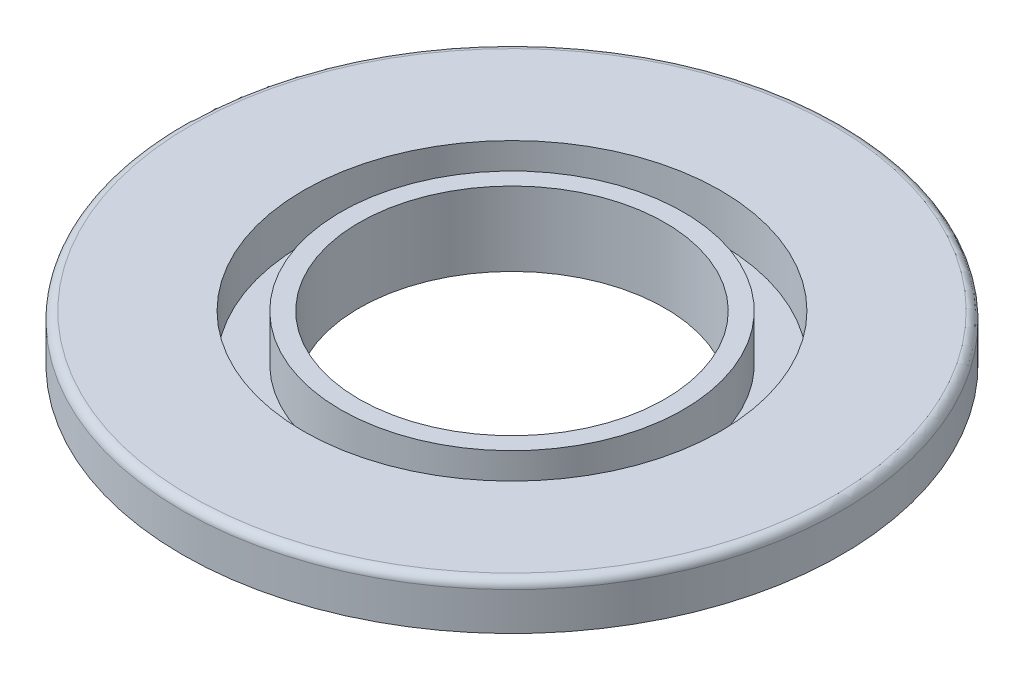
SolidWorks part; units mm, degrees
ref_plane "Front Plane" through (0, 0, 0) normal (0, 0, 1) x (1, 0, 0)
ref_plane "Top Plane" through (0, 0, 0) normal (0, 1, 0) x (1, 0, 0)
ref_plane "Right Plane" through (0, 0, 0) normal (1, 0, 0) x (0, 0, -1)
sketch "Sketch1" plane through (0, 0, 0) normal (0, 0, 1) x (1, 0, 0)
  line L0 (-54.8661, 40.6569) -> (-54.8661, 25.6579)
  line L1 (-54.8661, 25.6579) -> (-66.1427, 25.6579)
  line L2 (-66.1427, 25.6579) -> (-66.1427, 19.9648)
  line L3 (-66.1427, 19.9648) -> (-69.9745, 19.9648)
  line L5 (-71.8357, 31.2414) -> (-90.6666, 31.2414)
  line L6 (-90.6666, 31.2414) -> (-90.6666, 40.6569)
  line L7 (-90.6666, 40.6569) -> (-66.1427, 40.6569)
  line L8 (-66.1427, 40.6569) -> (-66.1427, 31.2414)
  line L9 (-66.1427, 31.2414) -> (-58.5884, 31.2414)
  line L10 (-58.5884, 31.2414) -> (-58.5884, 40.6569)
  line L11 (-58.5884, 40.6569) -> (-54.8661, 40.6569)
  line L12 (-69.9745, 19.9648) -> (-69.9745, 25.6579)
  line L13 (-69.9745, 25.6579) -> (-71.8357, 25.6579)
  line L14 (-71.8357, 25.6579) -> (-71.8357, 31.2414)
  line L15 (-23.8661, 40.6569) -> (-23.8661, 19.9648)
  dimension "D1" = 31
revolve "Revolve2" add sketch "Sketch1" angle 360 about L15
fillet "Fillet3" radius 1.7 1 edges at (-23.8661, 40.6569, 66.8006)
fillet "Fillet4" radius 1.7 1 edges at (-23.8661, 25.6579, 42.2766)
